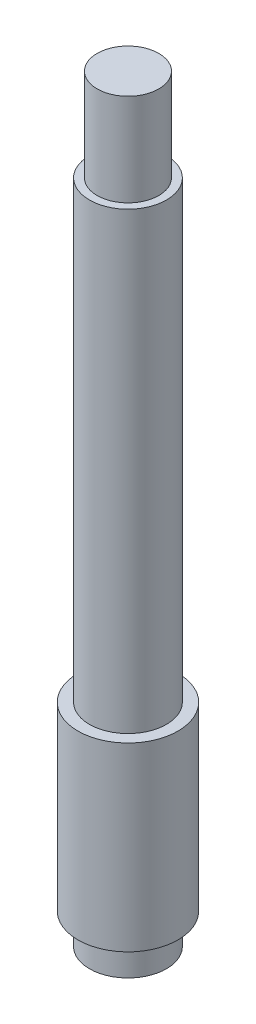
SolidWorks part; units mm, degrees
ref_plane "前基準面" through (0, 0, 0) normal (0, 0, 1) x (1, 0, 0)
ref_plane "上基準面" through (0, 0, 0) normal (0, 1, 0) x (1, 0, 0)
ref_plane "右基準面" through (0, 0, 0) normal (1, 0, 0) x (0, 0, -1)
sketch "草圖1" plane through (0, 0, 0) normal (0, 0, 1) x (1, 0, 0)
  line L0 (0, 463.3284) -> (0, -45.1049) construction
  line L1 (0, 0) -> (5, 0)
  line L2 (0, 0) -> (0, 98.5)
  line L3 (0, 98.5) -> (4, 98.5)
  line L7 (6.5, 27.5) -> (5, 27.5)
  line L8 (5, 86.5) -> (5, 27.5)
  line L12 (6.5, 27.5) -> (6.5, 4)
  line L14 (5, 0) -> (5, 4)
  line L15 (5, 4) -> (6.5, 4)
  line L19 (5, 86.5) -> (4, 86.5)
  line L20 (4, 98.5) -> (4, 86.5)
  dimension "D1" = 59
  dimension "D2" = 12
  dimension "D3" = 23.5
  dimension "D4" = 4
  dimension "D5" = 8
  dimension "D6" = 10
  dimension "D7" = 1.5
  dimension "D8" = 10
revolve "旋轉1" add sketch "草圖1" angle 360 about L0
